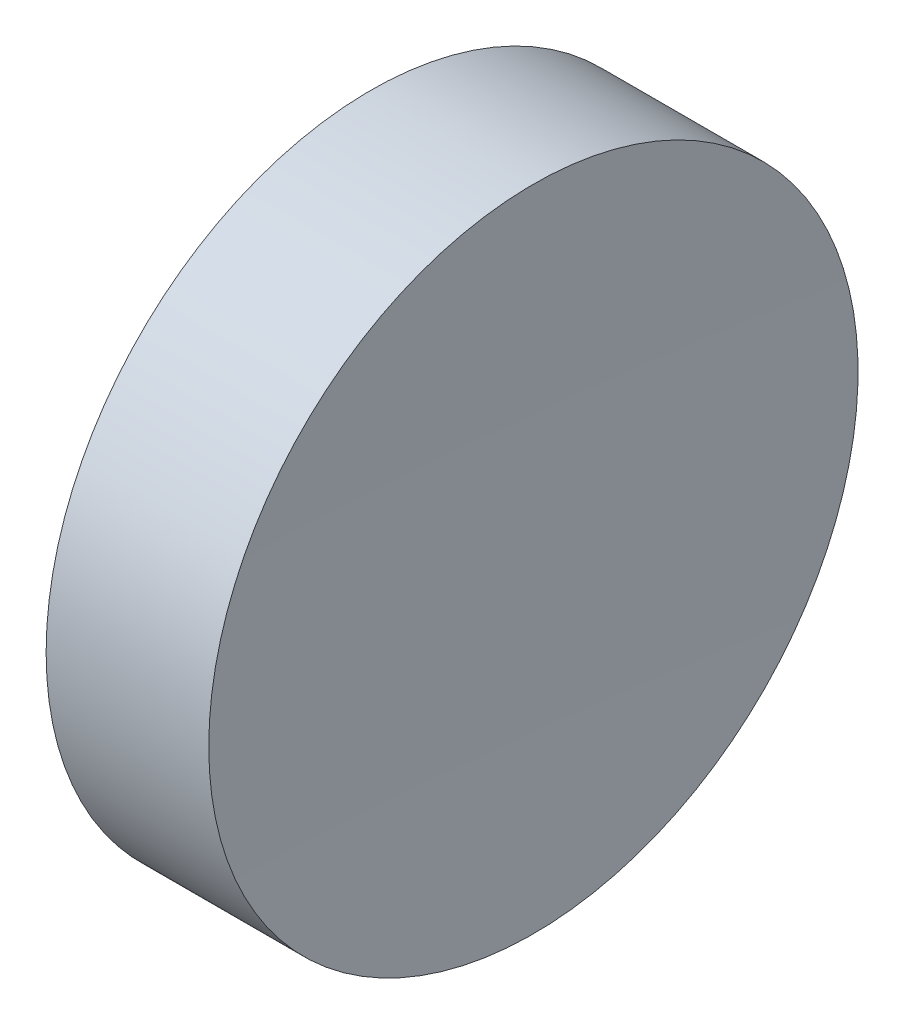
SolidWorks part; units mm, degrees
ref_plane "前视基准面" through (0, 0, 0) normal (0, 0, 1) x (1, 0, 0)
ref_plane "上视基准面" through (0, 0, 0) normal (0, 1, 0) x (1, 0, 0)
ref_plane "右视基准面" through (0, 0, 0) normal (1, 0, 0) x (0, 0, -1)
sketch "草图1" plane through (0, 0, 0) normal (0, 1, 0) x (1, 0, 0)
  line L0 (0, 0) -> (6.9328, 0) construction
  line L1 (0, 0) -> (3.08, 0)
  line L2 (0, 0) -> (0, 6.35)
  line L3 (0, 6.35) -> (3.1808, 6.35)
  arc A0 (3.1808, 6.35) -> (3.08, 0) centre (203.08, 0) ccw
  dimension "D3" = 200
  dimension "D1" = 3.08
  dimension "D2" = 6.35
revolve "旋转1" add sketch "草图1" angle 360 about L0
